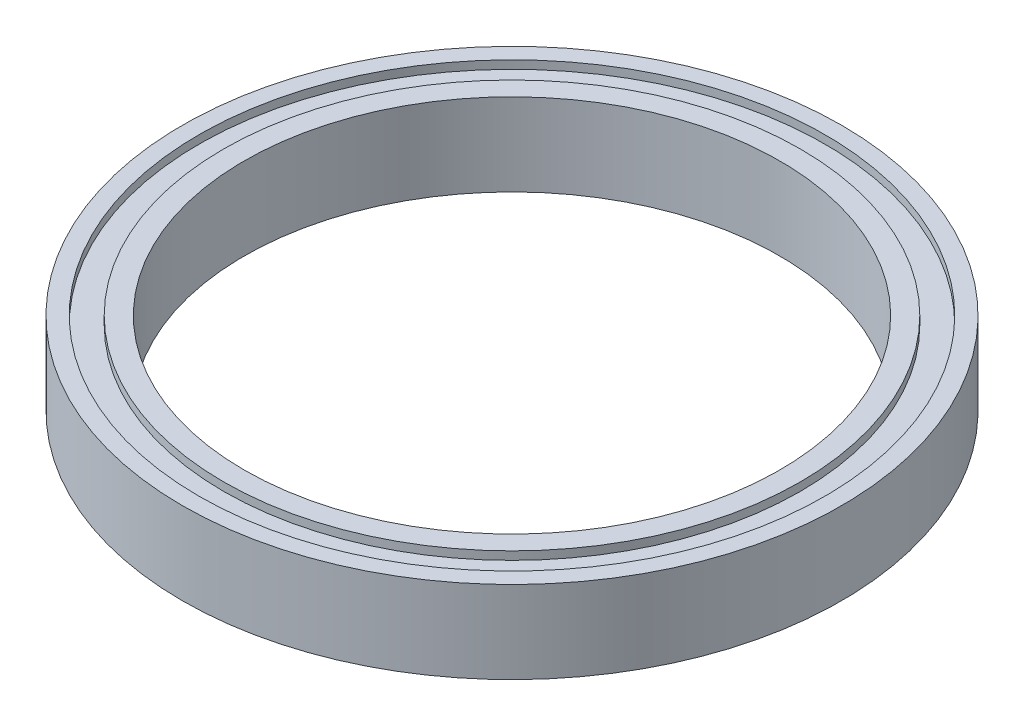
SolidWorks part; units mm, degrees
ref_plane "前视基准面" through (0, 0, 0) normal (0, 0, 1) x (1, 0, 0)
ref_plane "上视基准面" through (0, 0, 0) normal (0, 1, 0) x (1, 0, 0)
ref_plane "右视基准面" through (0, 0, 0) normal (1, 0, 0) x (0, 0, -1)
sketch "草图2" plane through (0, 0, 0) normal (0, 0, 1) x (1, 0, 0)
  line L0 (-38, 16.3039) -> (-38, 15.3039)
  line L1 (-40, 6.3039) -> (-38, 6.3039)
  line L2 (-40, 6.3039) -> (-40, 16.3039)
  line L3 (-40, 16.3039) -> (-38, 16.3039)
  line L4 (-32.5, 6.3039) -> (-32.5, 16.3039)
  line L5 (-40, 6.3039) -> (-32.5, 16.3039) construction
  line L6 (-40, 16.3039) -> (-32.5, 6.3039) construction
  line L7 (-38, 15.3039) -> (-35, 15.3039)
  line L8 (-35, 15.3039) -> (-35, 16.3039)
  line L9 (-38, 6.3039) -> (-38, 7.3039)
  line L10 (-38, 7.3039) -> (-35, 7.3039)
  line L11 (-35, 7.3039) -> (-35, 6.3039)
  line L12 (0, 37.4804) -> (0, -17.3403) construction
  line L13 (-35, 16.3039) -> (-32.5, 16.3039)
  line L14 (-35, 6.3039) -> (-32.5, 6.3039)
  point P0 (-36.25, 11.3039)
  point P12 (-38, 6.8039)
  point P15 (-38, 15.8039)
  dimension "D1" = 32.5
  dimension "D2" = 40
  dimension "D3" = 10
  dimension "D4" = 3
  dimension "D5" = 3
  dimension "D6" = 2
  dimension "D7" = 1
  dimension "D8" = 0.5
revolve "旋转1" add sketch "草图2" angle 360 about L12
